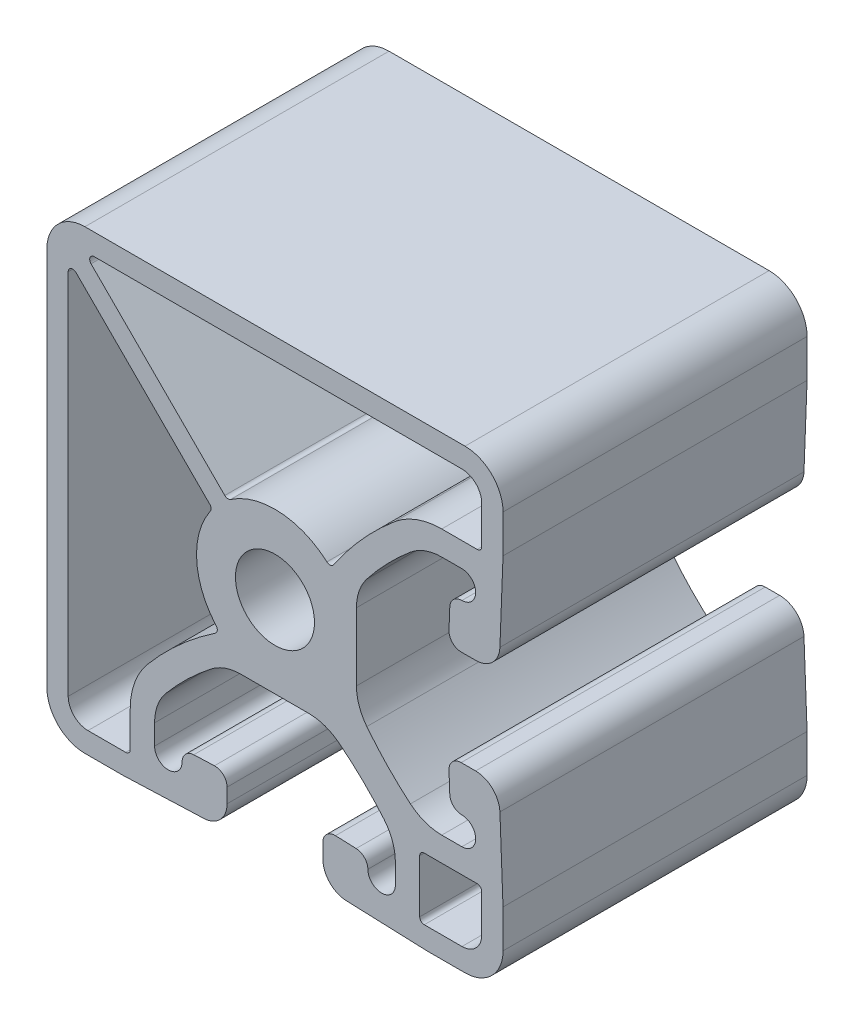
SolidWorks part; units mm, degrees
material "6061 Alloy"
ref_plane "Front" through (0, 0, 0) normal (0, 0, 1) x (1, 0, 0)
ref_plane "Top" through (0, 0, 0) normal (0, 1, 0) x (1, 0, 0)
ref_plane "Right" through (0, 0, 0) normal (1, 0, 0) x (0, 0, -1)
sketch "Sketch1" plane through (0, 0, 0) normal (0, 0, 1) x (1, 0, 0)
  line L0 (-4.1917, 5.4489) -> (-15.3644, 16.6216)
  line L1 (13.9316, 12.0904) -> (16.891, 12.0904)
  line L2 (15.621, 17.272) -> (-15.0949, 17.272)
  line L3 (17.272, 15.621) -> (17.272, 12.4714)
  line L4 (15.875, 19.05) -> (-15.875, 19.05)
  line L5 (-19.05, 15.875) -> (-19.05, -15.875)
  line L6 (19.05, 15.875) -> (19.05, 12.7)
  line L7 (19.05, 12.7) -> (18.7909, 5.9545)
  line L8 (-15.875, -19.05) -> (-12.7, -19.05)
  line L9 (-12.7, -19.05) -> (-5.9545, -18.7909)
  line L10 (15.5521, 4.0005) -> (16.7604, 4.0005)
  line L11 (-4.0005, -15.5521) -> (-4.0005, -16.7604)
  line L12 (14.6032, 6.7827) -> (14.5368, 5.0555)
  line L13 (-6.7827, -14.6032) -> (-5.0555, -14.5368)
  line L14 (13.9316, 10.0584) -> (15.6146, 10.0584)
  line L15 (-10.0584, -13.9316) -> (-10.0584, -15.6146)
  line L16 (6.8072, 2.8281) -> (6.8072, 0)
  line L17 (6.8072, -2.8281) -> (6.8072, 0)
  line L18 (-2.8281, -6.8072) -> (0, -6.8072)
  line L19 (2.8281, -6.8072) -> (0, -6.8072)
  line L20 (13.9316, -10.0584) -> (15.6146, -10.0584)
  line L21 (10.0584, -13.9316) -> (10.0584, -15.6146)
  line L22 (14.6032, -6.7827) -> (14.5368, -5.0555)
  line L23 (6.7827, -14.6032) -> (5.0555, -14.5368)
  line L24 (15.5521, -4.0005) -> (16.7604, -4.0005)
  line L25 (4.0005, -15.5521) -> (4.0005, -16.7604)
  line L26 (19.05, -12.7) -> (18.7909, -5.9545)
  line L27 (19.05, -15.875) -> (19.05, -12.7)
  line L28 (12.7, -19.05) -> (5.9545, -18.7909)
  line L29 (12.7, -19.05) -> (15.875, -19.05)
  line L30 (-5.4489, 4.1917) -> (-16.6216, 15.3644)
  line L31 (-17.272, 15.0949) -> (-17.272, -15.621)
  line L32 (-15.621, -17.272) -> (-12.4714, -17.272)
  line L33 (-12.0904, -13.9316) -> (-12.0904, -16.891)
  line L34 (12.4714, -12.0904) -> (16.891, -12.0904)
  line L35 (12.0904, -12.4714) -> (12.0904, -16.891)
  line L36 (17.272, -15.621) -> (17.272, -12.4714)
  line L37 (15.621, -17.272) -> (12.4714, -17.272)
  arc A0 (4.3383, 4.9116) -> (-3.7067, 5.4041) centre (0, 0) ccw
  arc A1 (4.3383, 4.9116) -> (4.9065, 4.9843) centre (4.5905, 5.1971) ccw
  arc A2 (-4.1917, 5.4489) -> (-3.7067, 5.4041) centre (-3.9223, 5.7183) ccw
  arc A3 (10.0091, 10.6607) -> (4.9065, 4.9843) centre (27.6606, -10.3378) ccw
  arc A4 (13.9316, 12.0904) -> (10.0091, 10.6607) centre (13.9316, 5.9944) ccw
  arc A5 (-15.0949, 17.272) -> (-15.3644, 16.6216) centre (-15.0949, 16.891) ccw
  arc A6 (16.891, 12.0904) -> (17.272, 12.4714) centre (16.891, 12.4714) ccw
  arc A7 (17.272, 15.621) -> (15.621, 17.272) centre (15.621, 15.621) ccw
  arc A8 (-15.875, 19.05) -> (-19.05, 15.875) centre (-15.875, 15.875) ccw
  arc A9 (19.05, 15.875) -> (15.875, 19.05) centre (15.875, 15.875) ccw
  arc A10 (-19.05, -15.875) -> (-15.875, -19.05) centre (-15.875, -15.875) ccw
  arc A11 (16.7604, 4.0005) -> (18.7909, 5.9545) centre (16.7604, 6.0325) ccw
  arc A12 (-5.9545, -18.7909) -> (-4.0005, -16.7604) centre (-6.0325, -16.7604) ccw
  arc A13 (14.5368, 5.0555) -> (15.5521, 4.0005) centre (15.5521, 5.0165) ccw
  arc A14 (-4.0005, -15.5521) -> (-5.0555, -14.5368) centre (-5.0165, -15.5521) ccw
  arc A15 (15.6167, 7.7597) -> (14.6032, 6.7827) centre (15.6184, 6.7437) ccw
  arc A16 (15.6167, 7.7597) -> (15.6146, 10.0584) centre (15.6146, 8.909) ccw
  arc A17 (-6.7827, -14.6032) -> (-7.7597, -15.6167) centre (-6.7437, -15.6184) ccw
  arc A18 (-10.0584, -15.6146) -> (-7.7597, -15.6167) centre (-8.909, -15.6146) ccw
  arc A19 (13.9316, 10.0584) -> (11.3166, 9.1053) centre (13.9316, 5.9944) ccw
  arc A20 (11.3166, 9.1053) -> (7.6732, 5.3359) centre (27.6606, -10.3378) ccw
  arc A21 (-9.1053, -11.3166) -> (-10.0584, -13.9316) centre (-5.9944, -13.9316) ccw
  arc A22 (7.6732, 5.3359) -> (6.8072, 2.8281) centre (10.8712, 2.8281) ccw
  arc A23 (-5.3359, -7.6732) -> (-9.1053, -11.3166) centre (10.3378, -27.6606) ccw
  arc A24 (-2.8281, -6.8072) -> (-5.3359, -7.6732) centre (-2.8281, -10.8712) ccw
  arc A25 (6.8072, -2.8281) -> (7.6732, -5.3359) centre (10.8712, -2.8281) ccw
  arc A26 (7.6732, -5.3359) -> (11.3166, -9.1053) centre (27.6606, 10.3378) ccw
  arc A27 (5.3359, -7.6732) -> (2.8281, -6.8072) centre (2.8281, -10.8712) ccw
  arc A28 (11.3166, -9.1053) -> (13.9316, -10.0584) centre (13.9316, -5.9944) ccw
  arc A29 (9.1053, -11.3166) -> (5.3359, -7.6732) centre (-10.3378, -27.6606) ccw
  arc A30 (10.0584, -13.9316) -> (9.1053, -11.3166) centre (5.9944, -13.9316) ccw
  arc A31 (15.6146, -10.0584) -> (15.6167, -7.7597) centre (15.6146, -8.909) ccw
  arc A32 (14.6032, -6.7827) -> (15.6167, -7.7597) centre (15.6184, -6.7437) ccw
  arc A33 (7.7597, -15.6167) -> (10.0584, -15.6146) centre (8.909, -15.6146) ccw
  arc A34 (7.7597, -15.6167) -> (6.7827, -14.6032) centre (6.7437, -15.6184) ccw
  arc A35 (15.5521, -4.0005) -> (14.5368, -5.0555) centre (15.5521, -5.0165) ccw
  arc A36 (5.0555, -14.5368) -> (4.0005, -15.5521) centre (5.0165, -15.5521) ccw
  arc A37 (18.7909, -5.9545) -> (16.7604, -4.0005) centre (16.7604, -6.0325) ccw
  arc A38 (4.0005, -16.7604) -> (5.9545, -18.7909) centre (6.0325, -16.7604) ccw
  arc A39 (15.875, -19.05) -> (19.05, -15.875) centre (15.875, -15.875) ccw
  arc A40 (-16.6216, 15.3644) -> (-17.272, 15.0949) centre (-16.891, 15.0949) ccw
  arc A41 (-5.4041, 3.7067) -> (-5.4489, 4.1917) centre (-5.7183, 3.9223) ccw
  arc A42 (-5.4041, 3.7067) -> (-4.9116, -4.3383) centre (0, 0) ccw
  arc A43 (-17.272, -15.621) -> (-15.621, -17.272) centre (-15.621, -15.621) ccw
  arc A44 (-4.9843, -4.9065) -> (-4.9116, -4.3383) centre (-5.1971, -4.5905) ccw
  arc A45 (-4.9843, -4.9065) -> (-10.6607, -10.0091) centre (10.3378, -27.6606) ccw
  arc A46 (-12.4714, -17.272) -> (-12.0904, -16.891) centre (-12.4714, -16.891) ccw
  arc A47 (-10.6607, -10.0091) -> (-12.0904, -13.9316) centre (-5.9944, -13.9316) ccw
  circle A48 centre (0, 0) radius 3.302
  arc A49 (12.4714, -12.0904) -> (12.0904, -12.4714) centre (12.4714, -12.4714) ccw
  arc A50 (17.272, -12.4714) -> (16.891, -12.0904) centre (16.891, -12.4714) ccw
  arc A51 (12.0904, -16.891) -> (12.4714, -17.272) centre (12.4714, -16.891) ccw
  arc A52 (15.621, -17.272) -> (17.272, -15.621) centre (15.621, -15.621) ccw
extrude "Extrude1" add sketch "Sketch1" along normal blind 25.4
